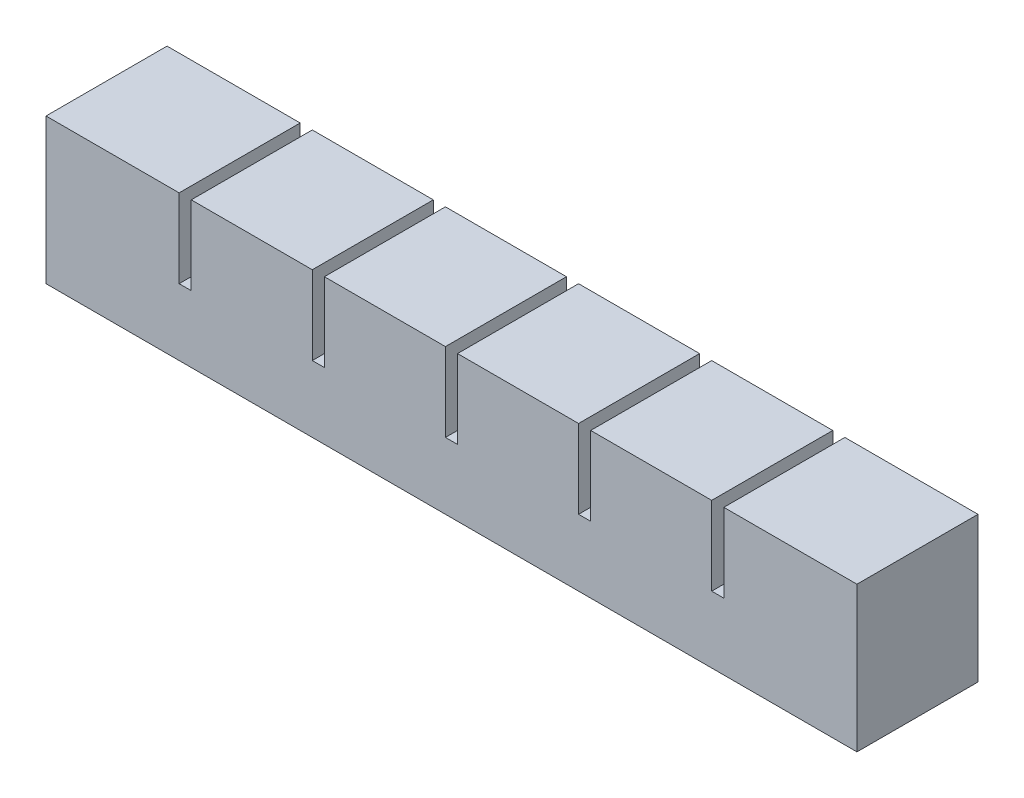
SolidWorks part; units mm, degrees
ref_plane "Front Plane" through (0, 0, 0) normal (0, 0, 1) x (1, 0, 0)
ref_plane "Top Plane" through (0, 0, 0) normal (0, 1, 0) x (1, 0, 0)
ref_plane "Right Plane" through (0, 0, 0) normal (1, 0, 0) x (0, 0, -1)
sketch "Sketch1" plane through (0, 0, 0) normal (0, 0, 1) x (1, 0, 0)
  line L1 (0, 0) -> (20, 0)
  line L2 (0, 0) -> (0, 18)
  line L3 (0, 18) -> (20, 18)
  line L4 (20, 0) -> (20, 18)
  dimension "D1" = 20
  dimension "D2" = 18
extrude "Boss-Extrude1" add sketch "Sketch1" along normal blind 20
sketch "Sketch2" plane through (0, 0, 0) normal (0, -1, 0) x (1, 0, 0)
  line L0 (20, 20) -> (20, 0) construction
  line L1 (4, 16) -> (16, 16)
  line L2 (4, 16) -> (4, 4)
  line L3 (4, 4) -> (16, 4)
  line L4 (16, 16) -> (16, 4)
  line L5 (0, 20) -> (20, 20) construction
  line L6 (0, 20) -> (0, 0) construction
  line L7 (0, 0) -> (20, 0) construction
  dimension "D1" = 4
  dimension "D2" = 4
  dimension "D3" = 4
  dimension "D4" = 4
extrude "Cut-Extrude1" cut sketch "Sketch2" against normal blind 14
sketch "Sketch3" plane through (20, 0, 0) normal (1, 0, 0) x (0, 0, -1)
  line L0 (0, 0) -> (0, 18) construction
  line L1 (-20, 0) -> (0, 0)
  line L2 (-20, 0) -> (-20, 5)
  line L3 (-20, 5) -> (0, 5)
  line L4 (0, 0) -> (0, 5)
  dimension "D1" = 5
extrude "Boss-Extrude2" add sketch "Sketch3" along normal blind 2
pattern_linear "LPattern1" count 6 spacing 22 along (1, 0, 0) of bodies 103
combine bodies "Combine1" operation type add bodies to combine 107 108 103 104 105 106
sketch "Sketch4" plane through (130, 0, 0) normal (1, 0, 0) x (0, 0, -1)
  line L1 (-20, 5) -> (0, 5)
  line L2 (-20, 5) -> (-20, 18)
  line L3 (-20, 18) -> (0, 18)
  line L4 (0, 5) -> (0, 18)
extrude "Boss-Extrude3" add sketch "Sketch4" along normal up to surface (2 mm away) up to face at (132, 2.5, 10)
sketch "Sketch5" plane through (0, 0, 0) normal (-1, 0, 0) x (0, 0, 1)
  line L1 (0, 18) -> (20, 18)
  line L2 (0, 18) -> (0, 0)
  line L3 (0, 0) -> (20, 0)
  line L4 (20, 18) -> (20, 0)
extrude "Boss-Extrude4" add sketch "Sketch5" along normal blind 2
ref_point "Point1"
sketch "Sketch6" plane through (0, 0, 0) normal (0, -1, 0) x (-1, 0, 0)
  line L0 (-126, -4) -> (-126, -16) construction
  line L1 (-4, -9) -> (-126, -9)
  line L2 (-4, -9) -> (-4, -11)
  line L3 (-4, -11) -> (-126, -11)
  line L4 (-126, -9) -> (-126, -11)
  line L5 (-4, -9) -> (-126, -11) construction
  line L6 (-4, -11) -> (-126, -9) construction
  point P0 (-65, -10)
  dimension "D1" = 2
extrude "Cut-Extrude2" cut sketch "Sketch6" against normal blind 2
sketch "Sketch7" plane through (0, 0, 0) normal (0, -1, 0) x (-1, 0, 0)
  line L1 (2, -20) -> (-132, -20)
  line L2 (2, -20) -> (2, 0)
  line L3 (2, 0) -> (-132, 0)
  line L4 (-132, -20) -> (-132, 0)
extrude "Boss-Extrude5" add sketch "Sketch7" along normal blind 6
